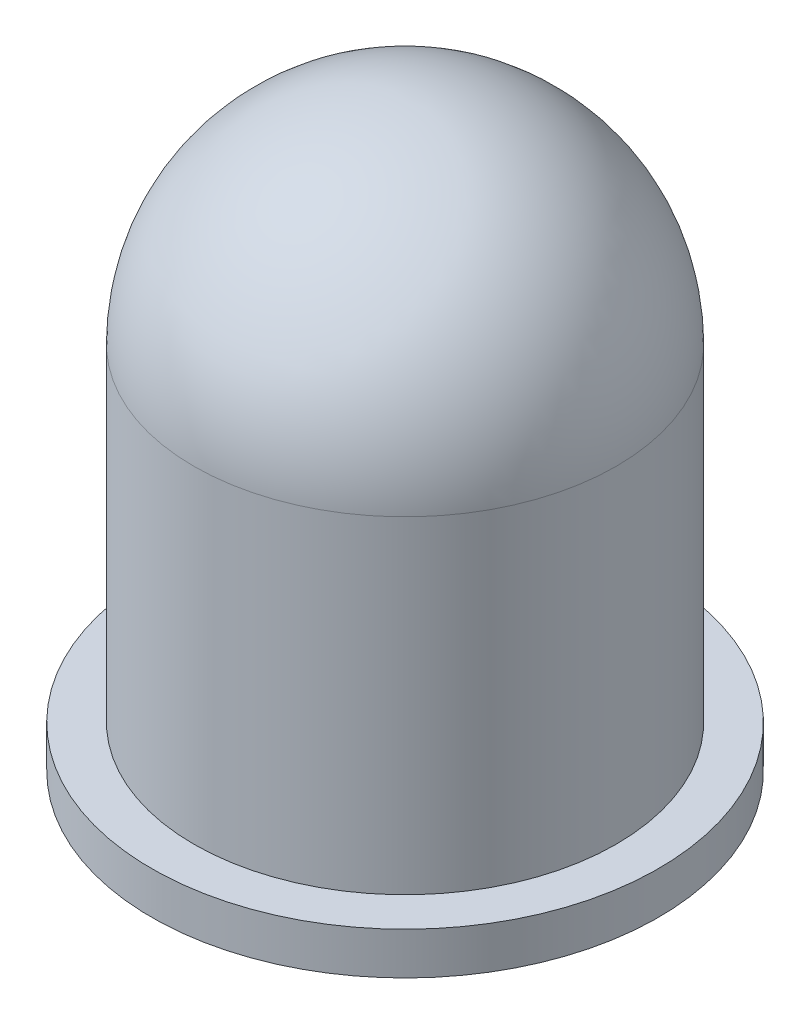
SolidWorks part; units mm, degrees
material "Epoxy, Unfilled"
ref_plane "Front Plane" through (0, 0, 0) normal (0, 0, 1) x (1, 0, 0)
ref_plane "Top Plane" through (0, 0, 0) normal (0, 1, 0) x (1, 0, 0)
ref_plane "Right Plane" through (0, 0, 0) normal (1, 0, 0) x (0, 0, -1)
sketch "Sketch1" plane through (0, 0, 0) normal (0, 0, 1) x (1, 0, 0)
  line L0 (0, 0) -> (4.8, 0)
  line L1 (4.8, 0) -> (4.8, 0.8)
  line L2 (4.8, 0.8) -> (4, 0.8)
  line L3 (4, 0.8) -> (4, 7)
  line L4 (0, 0) -> (0, 11)
  arc A0 (4, 7) -> (0, 11) centre (0, 7) ccw
  point P8 (0, 5.1372)
  point P9 (0, 0)
  dimension "D1" = 4
  dimension "D2" = 0.8
  dimension "D3" = 0.8
  dimension "D4" = 11
revolve "Revolve1" add sketch "Sketch1" angle 360 about L4
